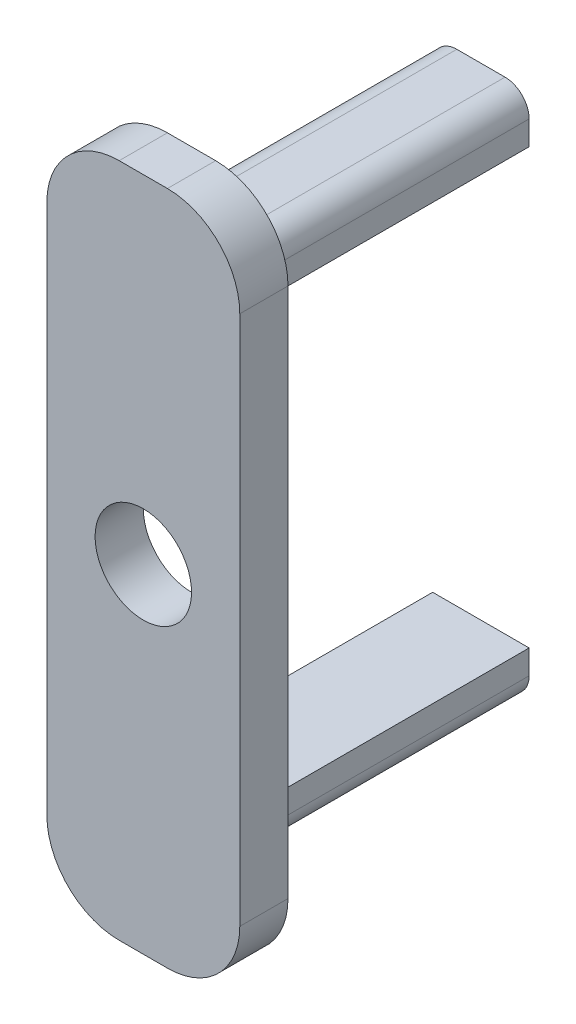
SolidWorks part; units mm, degrees
ref_plane "Front Plane" through (0, 0, 0) normal (0, 0, 1) x (1, 0, 0)
ref_plane "Top Plane" through (0, 0, 0) normal (0, 1, 0) x (1, 0, 0)
ref_plane "Right Plane" through (0, 0, 0) normal (1, 0, 0) x (0, 0, -1)
sketch "Sketch1" plane through (0, 0, 0) normal (0, 0, 1) x (1, 0, 0)
  line L1 (4, -14) -> (-4, -14)
  line L2 (4, -14) -> (4, 14)
  line L3 (4, 14) -> (-4, 14)
  line L4 (-4, -14) -> (-4, 14)
  line L5 (4, -14) -> (-4, 14) construction
  line L6 (4, 14) -> (-4, -14) construction
  point P0 (0, 0)
  dimension "D1" = 8
  dimension "D2" = 28
extrude "Boss-Extrude1" add sketch "Sketch1" along normal blind 2
fillet "Fillet1" radius 3 4 edges at (-4, -14, 1) (4, -14, 1) (-4, 14, 1) (4, 14, 1)
sketch "Sketch2" plane through (0, 0, 0) normal (0, 0, -1) x (-1, 0, 0)
  line L0 (-4, -11) -> (-4, 11) construction
  line L1 (4, -9) -> (-4, -9)
  line L2 (4, -9) -> (4, 9)
  line L3 (4, 9) -> (-4, 9)
  line L4 (-4, -9) -> (-4, 9)
  line L5 (4, 11) -> (4, -11) construction
  line L7 (2, 9) -> (2, 11)
  line L8 (2, 11) -> (-2, 11)
  line L9 (-2, 9) -> (-2, 11)
  line L10 (0, 9) -> (2, 9.3642) construction
  line L11 (2, 11) -> (0, 9) construction
  line L12 (-1, 14) -> (1, 14) construction
  line L13 (-2, 9) -> (2, 9)
  line L14 (-4, 0) -> (4, 0) construction
  line L15 (-2, -9) -> (-2, -11)
  line L16 (2, -11) -> (-2, -11)
  line L17 (2, -9) -> (2, -11)
  line L18 (-2, -9) -> (2, -9)
  point P0 (0, 0)
  point P8 (0, 9)
  dimension "D2" = 2
  dimension "D1" = 18
  dimension "D3" = 4
  dimension "D4" = 2
  dimension "D5" = 5
extrude "Boss-Extrude2" add sketch "Sketch2" along normal blind 12 contours L9 L3 L7 L8 | L17 L1 L15 L16
fillet "Fillet2" radius 1 4 edges at (-2, -11, -6) (2, -11, -6) (-2, 11, -6) (2, 11, -6)
sketch "Sketch3" plane through (0, 0, 0) normal (0, 0, -1) x (-1, 0, 0)
  circle A0 centre (0, 0) radius 2
  dimension "D1" = 4
extrude "Cut-Extrude3" cut sketch "Sketch3" against normal blind 10
